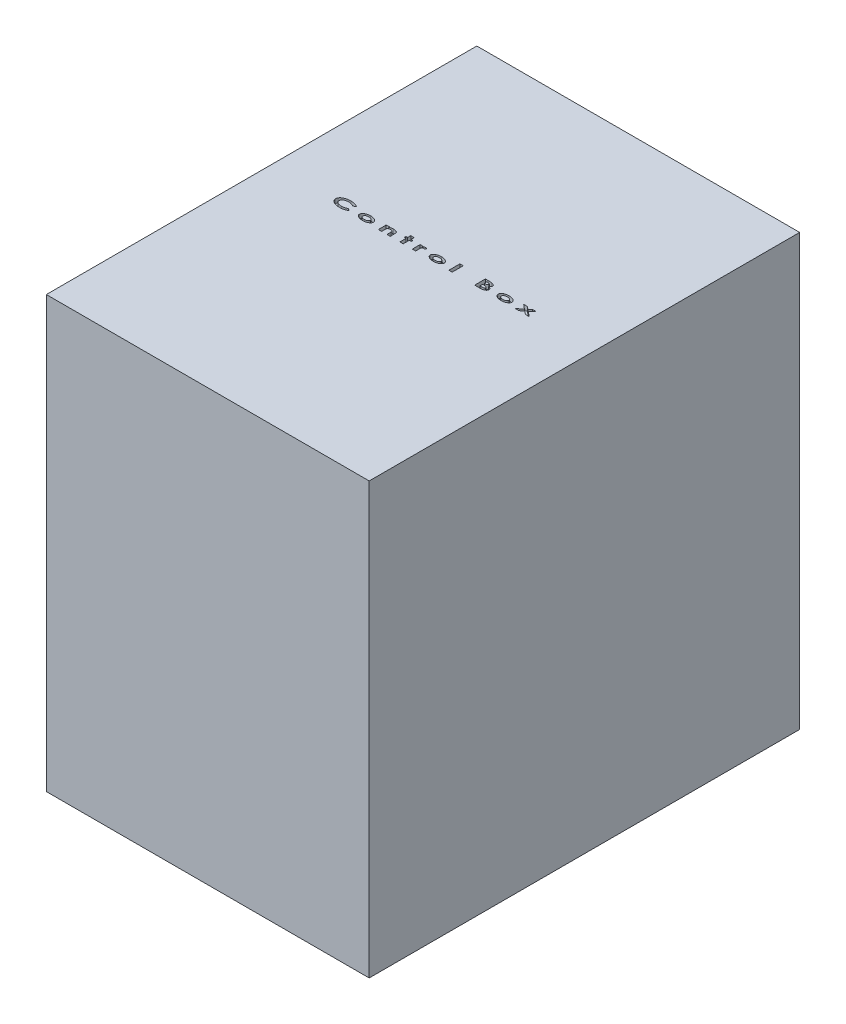
SolidWorks part; units mm, degrees
ref_plane "Front Plane" through (0, 0, 0) normal (0, 0, 1) x (1, 0, 0)
ref_plane "Top Plane" through (0, 0, 0) normal (0, 1, 0) x (1, 0, 0)
ref_plane "Right Plane" through (0, 0, 0) normal (1, 0, 0) x (0, 0, -1)
sketch "Sketch1" plane through (0, 0, 0) normal (0, 1, 0) x (1, 0, 0)
  line L0 (-71.6129, -95.9677) -> (-71.6129, 104.0323)
  line L1 (-71.6129, 104.0323) -> (78.3871, 104.0323)
  line L7 (-71.6129, -95.9677) -> (78.3871, -95.9677)
  line L8 (78.3871, 104.0323) -> (78.3871, -95.9677)
  dimension "D1" = 150
  dimension "D2" = 200
extrude "Boss-Extrude1" add sketch "Sketch1" along normal blind 200
sketch "Sketch5" plane through (0, 200, 0) normal (0, 1, 0) x (1, 0, 0)
  text T0 "<b>Control Box</b>" font "Century Gothic" height 5
extrude "Cut-Extrude1" cut sketch "Sketch5" against normal blind 2
